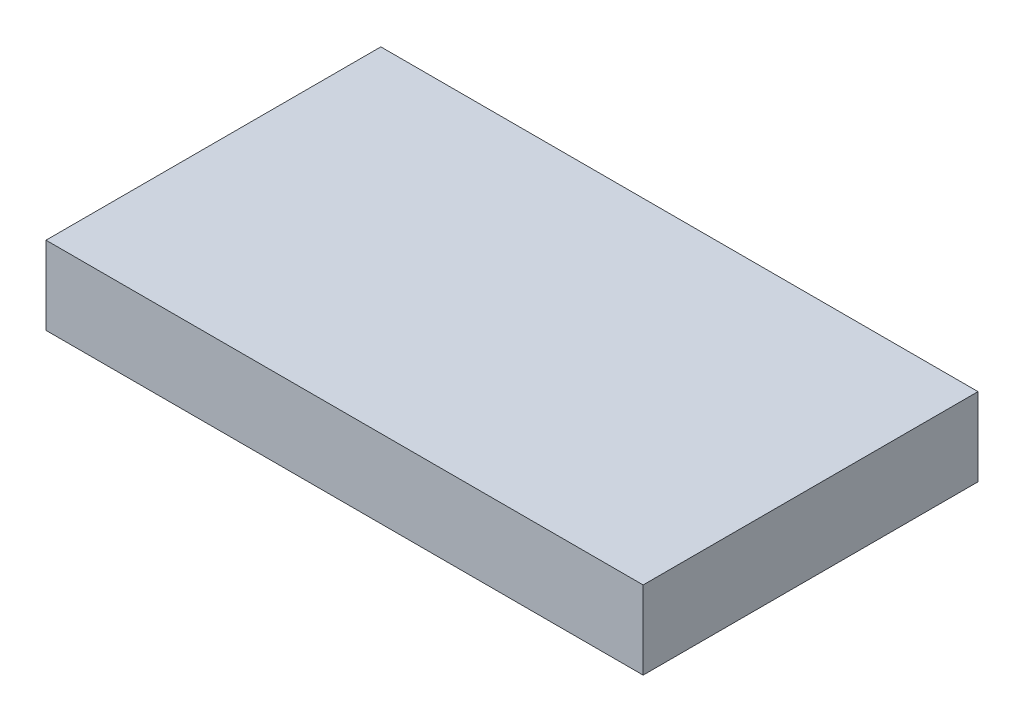
SolidWorks part; units mm, degrees
ref_plane "Front Plane" through (0, 0, 0) normal (0, 0, 1) x (1, 0, 0)
ref_plane "Top Plane" through (0, 0, 0) normal (0, 1, 0) x (1, 0, 0)
ref_plane "Right Plane" through (0, 0, 0) normal (1, 0, 0) x (0, 0, -1)
sketch "Sketch1" plane through (0, 0, 0) normal (0, 1, 0) x (1, 0, 0)
  line L1 (0, 0) -> (-53.5, 0)
  line L2 (0, 0) -> (0, -30)
  line L3 (0, -30) -> (-53.5, -30)
  line L4 (-53.5, 0) -> (-53.5, -30)
  dimension "D1" = 30
  dimension "D2" = 53.5
extrude "Boss-Extrude1" add sketch "Sketch1" along normal blind 7
